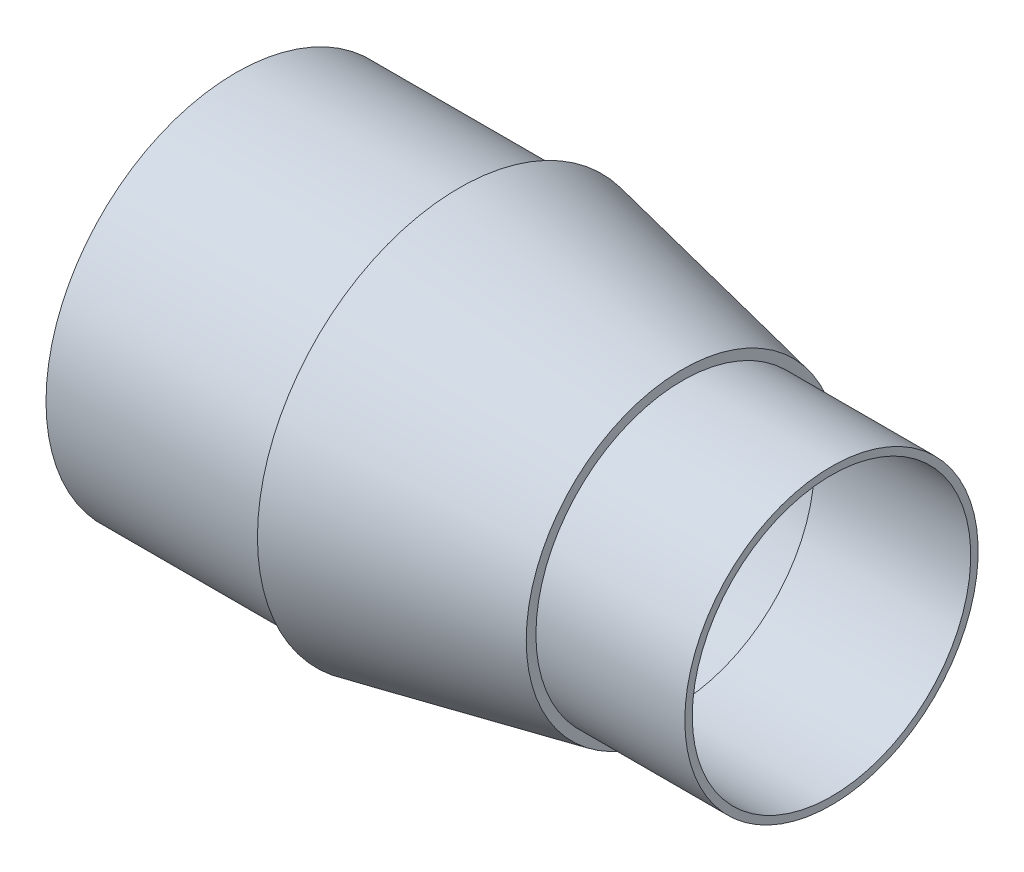
SolidWorks part; units mm, degrees
ref_plane "Front Plane" through (0, 0, 0) normal (0, 0, 1) x (1, 0, 0)
ref_plane "Top Plane" through (0, 0, 0) normal (0, 1, 0) x (1, 0, 0)
ref_plane "Right Plane" through (0, 0, 0) normal (1, 0, 0) x (0, 0, -1)
sketch "Sketch1" plane through (0, 0, 0) normal (0, 1, 0) x (1, 0, 0)
  line L2 (76.2, 68.834) -> (152.4, 53.34)
  line L3 (0, 64.77) -> (0, 0)
  line L5 (0, 0) -> (203.2, 0)
  line L7 (76.2, 68.834) -> (76.2, 53.34) construction
  line L8 (76.2, 53.34) -> (152.4, 53.34) construction
  line L9 (152.4, 50.038) -> (203.2, 50.038)
  line L10 (152.4, 53.34) -> (152.4, 50.038)
  line L11 (76.2, 68.834) -> (76.2, 64.77)
  line L12 (76.2, 64.77) -> (0, 64.77)
  line L13 (203.2, 50.038) -> (203.2, 0)
  dimension "D1" = 64.77
  dimension "D2" = 50.038
  dimension "D3" = 76.2
  dimension "D4" = 50.8
  dimension "D5" = 76.2
  dimension "D6" = 4.064
  dimension "D7" = 3.302
revolve "Revolve1" add sketch "Sketch1" angle 360 about L5
shell "Shell1" thickness 2.54
